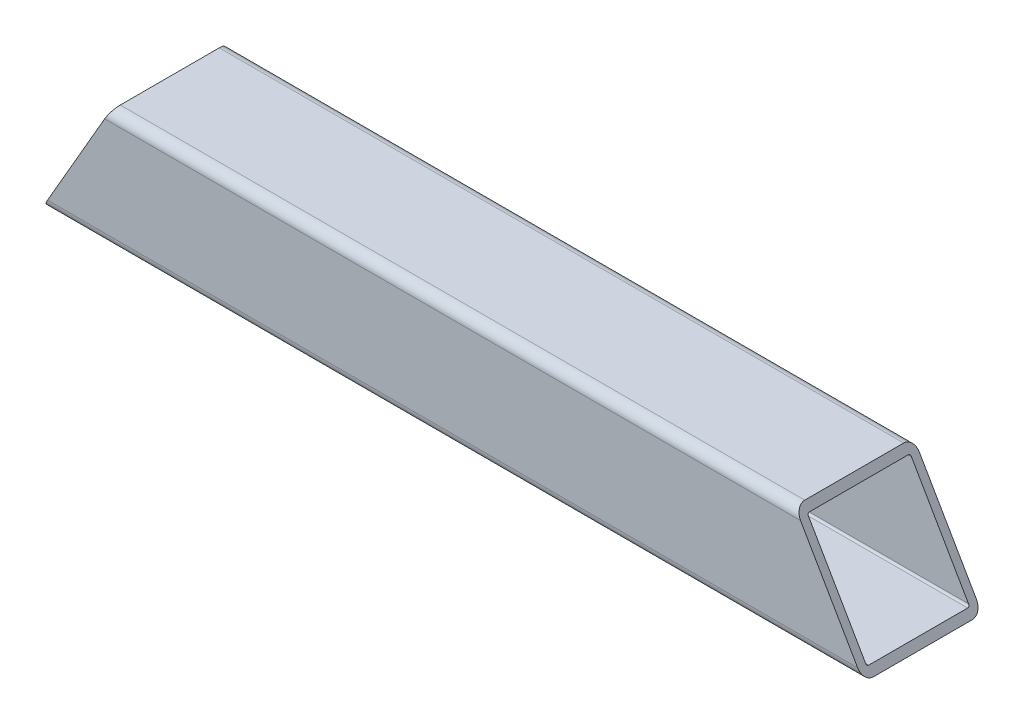
SolidWorks part; units mm, degrees
ref_plane "Front Plane" through (0, 0, 0) normal (0, 0, 1) x (1, 0, 0)
ref_plane "Top Plane" through (0, 0, 0) normal (0, 1, 0) x (1, 0, 0)
ref_plane "Right Plane" through (0, 0, 0) normal (1, 0, 0) x (0, 0, -1)
sketch "Sketch1" plane through (0, 0, 0) normal (1, 0, 0) x (0, 0, -1)
  line L1 (-15.875, 19.05) -> (15.875, 19.05)
  line L2 (-19.05, 15.875) -> (-19.05, -15.875)
  line L3 (-15.875, -19.05) -> (15.875, -19.05)
  line L4 (19.05, 15.875) -> (19.05, -15.875)
  line L5 (-19.05, 19.05) -> (19.05, -19.05) construction
  line L6 (-19.05, -19.05) -> (19.05, 19.05) construction
  arc A0 (-19.05, -15.875) -> (-15.875, -19.05) centre (-15.875, -15.875) ccw
  arc A1 (15.875, -19.05) -> (19.05, -15.875) centre (15.875, -15.875) ccw
  arc A2 (19.05, 15.875) -> (15.875, 19.05) centre (15.875, 15.875) ccw
  arc A3 (-15.875, 19.05) -> (-19.05, 15.875) centre (-15.875, 15.875) ccw
  point P0 (0, 0)
  dimension "D3" = 3.175
  dimension "D1" = 38.1
  dimension "D2" = 38.1
extrude "Extrude-Thin1" add sketch "Sketch1" along normal mid plane 263.525 thin
sketch "Sketch2" plane through (0, 0, 19.05) normal (0, 0, 1) x (1, 0, 0)
  line L0 (-131.7625, -19.05) -> (-109.7655, 19.05)
  line L1 (131.7625, 19.05) -> (-131.7625, 19.05) construction
  line L2 (-131.7625, 15.875) -> (-131.7625, -15.875) construction
  dimension "D1" = 30
extrude "Cut-Extrude1" cut sketch "Sketch2" against normal through all and the other way through all
sketch "Sketch3" plane through (0, 0, 19.05) normal (0, 0, 1) x (1, 0, 0)
  line L0 (131.7625, -19.05) -> (109.7655, 19.05)
  line L1 (131.7625, 19.05) -> (-109.7655, 19.05) construction
  line L2 (131.7625, 15.875) -> (131.7625, -15.875) construction
  dimension "D1" = 30
extrude "Cut-Extrude2" cut sketch "Sketch3" against normal through all and the other way through all flip side to cut
